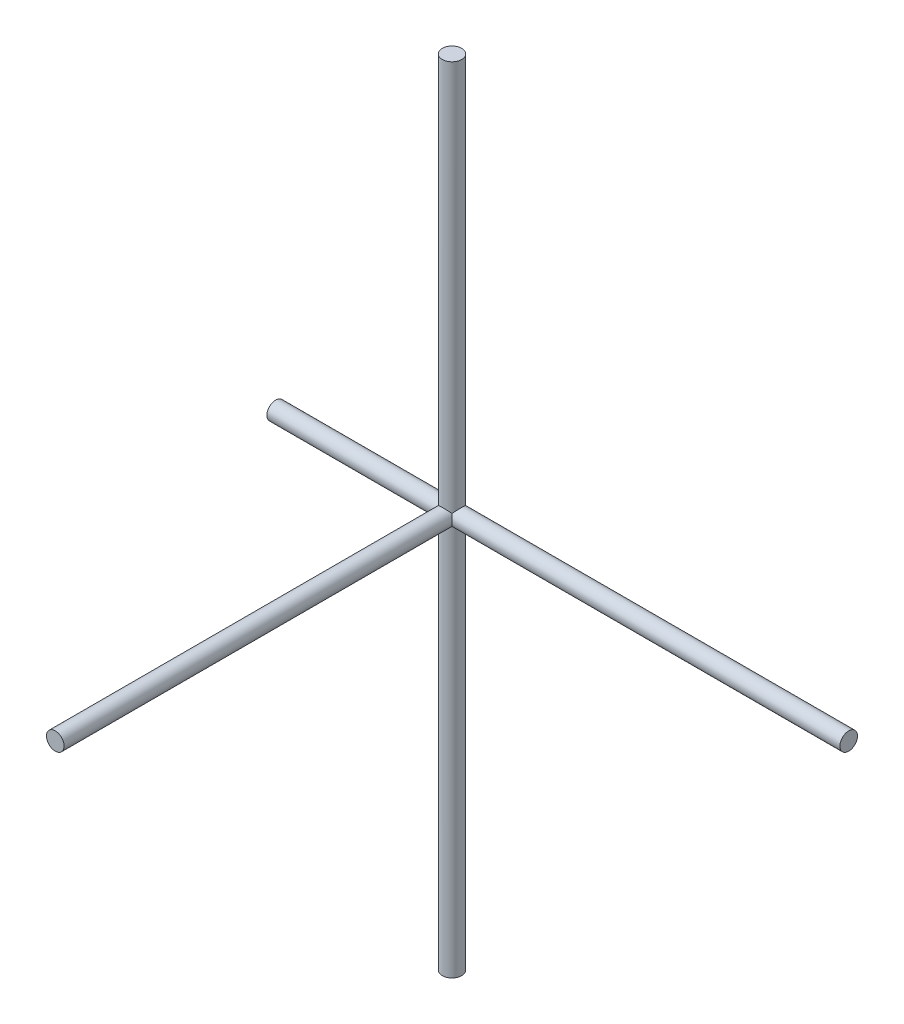
SolidWorks part; units mm, degrees
ref_plane "Alzado" through (0, 0, 0) normal (0, 0, 1) x (1, 0, 0)
ref_plane "Planta" through (0, 0, 0) normal (0, 1, 0) x (1, 0, 0)
ref_plane "Vista lateral" through (0, 0, 0) normal (1, 0, 0) x (0, 0, -1)
sketch "Croquis1" plane through (0, 0, 0) normal (0, 1, 0) x (1, 0, 0)
  circle A0 centre (0, 0) radius 4.4
extrude "Saliente-Extruir1" add sketch "Croquis1" along normal blind 180
sketch "Croquis4" plane through (0, 0, 0) normal (0, -1, 0) x (-1, 0, 0)
  circle A0 centre (0, 0) radius 4.4
extrude "Saliente-Extruir2" add sketch "Croquis4" along normal blind 180
sketch "Croquis5" plane through (0, 0, 0) normal (1, 0, 0) x (0, 0, -1)
  circle A0 centre (0, 0) radius 4
extrude "Saliente-Extruir3" add sketch "Croquis5" along normal blind 180
sketch "Croquis6" plane through (0, 0, 0) normal (1, 0, 0) x (0, 0, -1)
  circle A0 centre (0, 0) radius 4
extrude "Saliente-Extruir4" add sketch "Croquis6" against normal blind 80
sketch "Croquis7" plane through (0, 0, 0) normal (0, 0, 1) x (1, 0, 0)
  circle A0 centre (0, 0) radius 4
extrude "Saliente-Extruir5" add sketch "Croquis7" along normal blind 180
sketch "Croquis8" plane through (0, 180, 0) normal (0, 1, 0) x (1, 0, 0)
  circle A0 centre (0, 0) radius 4.4
